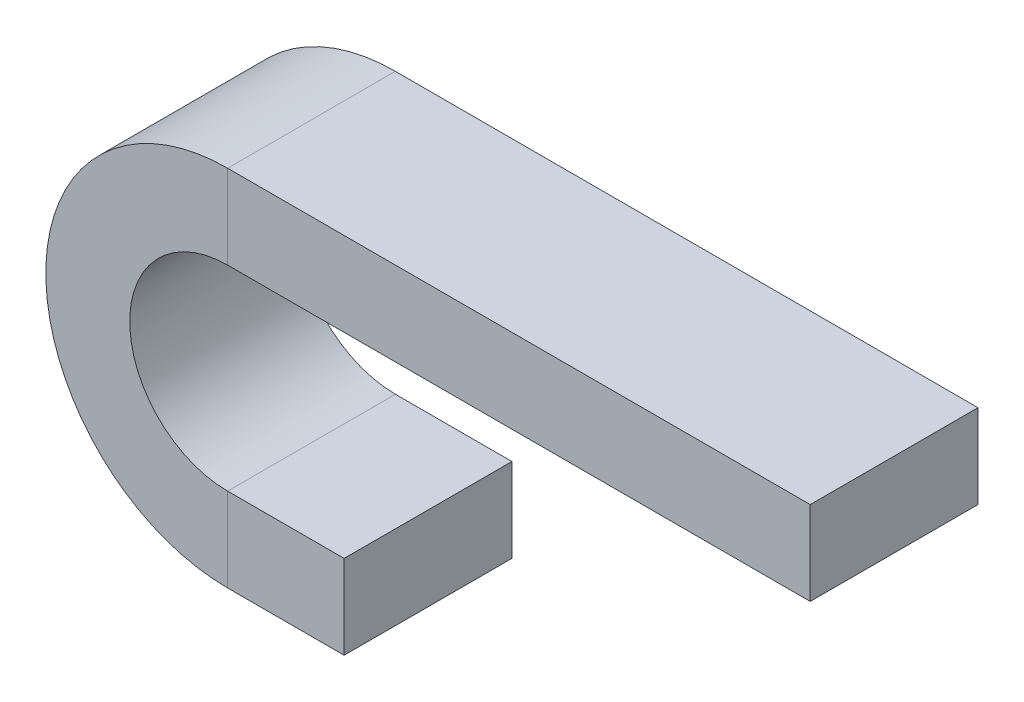
SolidWorks part; units mm, degrees
ref_plane "Front" through (0, 0, 0) normal (0, 0, 1) x (1, 0, 0)
ref_plane "Top" through (0, 0, 0) normal (0, 1, 0) x (1, 0, 0)
ref_plane "Right" through (0, 0, 0) normal (1, 0, 0) x (0, 0, -1)
sketch "Sketch1" plane through (0, 0, 0) normal (0, 0, 1) x (1, 0, 0)
  line L0 (0, 0) -> (-50, 0)
  line L1 (-50, 120) -> (200, 120)
  arc A0 (-50, 0) -> (-50, 120) centre (-50, 60) cw
  dimension "D2" = 60
  dimension "D1" = 50
  dimension "D3" = 250
sketch "Sketch2" plane through (0, 0, 0) normal (1, 0, 0) x (0, 0, -1)
  line L1 (36, -18) -> (-36, -18)
  line L2 (36, -18) -> (36, 18)
  line L3 (36, 18) -> (-36, 18)
  line L4 (-36, -18) -> (-36, 18)
  line L5 (36, -18) -> (-36, 18) construction
  line L6 (36, 18) -> (-36, -18) construction
  point P0 (0, 0)
  dimension "D2" = 72
  dimension "36" = 36
sweep "Sweep1" add profiles "Sketch2" path "Sketch1"
